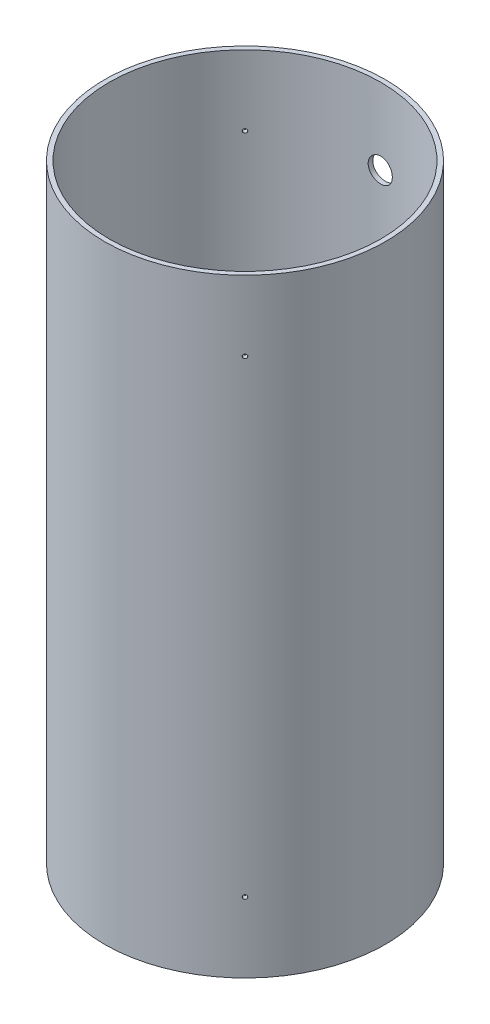
SolidWorks part; units mm, degrees
material "A-Glass Fiber"
ref_plane "Front Plane" through (0, 0, 0) normal (0, 0, 1) x (1, 0, 0)
ref_plane "Top Plane" through (0, 0, 0) normal (0, 1, 0) x (1, 0, 0)
ref_plane "Right Plane" through (0, 0, 0) normal (1, 0, 0) x (0, 0, -1)
sketch "Sketch1" plane through (0, 0, 0) normal (0, 1, 0) x (1, 0, 0)
  circle A0 centre (0, 0) radius 76.1746
  circle A1 centre (0, 0) radius 73.66
  dimension "D1" = 152.3492
  dimension "D2" = 147.32
extrude "Boss-Extrude1" add sketch "Sketch1" along normal blind 330.2
sketch "Sketch4" plane through (0, 0, 0) normal (0, 0, 1) x (1, 0, 0)
  line L0 (-76.1746, 0) -> (76.1746, 0) construction
  line L1 (76.1746, 330.2) -> (-76.1746, 330.2) construction
  line L2 (0, 330.2) -> (0, 0) construction
  line L3 (73.66, 330.2) -> (-73.66, 330.2) construction
  point P0 (0, 41.275)
  point P3 (0, 288.925)
  dimension "D1" = 41.275
  dimension "D2" = 41.275
hole_wizard "1/2 Clearance Hole5" positions "Sketch16" profile "Sketch17" hole size "1/2" standard "ANSI Inch"
sketch "Sketch16" plane through (0, 0, 0) normal (0, 0, 1) x (1, 0, 0)
  point P0 (0, 288.925)
sketch "Sketch17" plane through (0, 288.925, 0) normal (1, 0, 0) x (0, -1, 0)
  line L0 (0, 0) -> (0, 80.1345)
  line L1 (0, 80.1345) -> (6.5481, 76.2)
  line L2 (6.5481, 76.2) -> (6.5481, 0)
  line L5 (6.5481, 0) -> (0, 0)
  line L10 (0, 80.1345) -> (-6.5481, 76.2) construction
  line L11 (0, -6.35) -> (0, 107.95) construction
  dimension "Hole Dia." = 13.0962
  dimension "Hole Depth" = 76.2
  dimension "Drill Angle" = 118
hole_wizard "1/2 Clearance Hole7" positions "Sketch20" profile "Sketch21" hole size "1/2" standard "ANSI Inch"
sketch "Sketch20" plane through (0, 0, 0) normal (0, 0, 1) x (1, 0, 0)
  point P0 (0, 41.275)
sketch "Sketch21" plane through (0, 41.275, 0) normal (1, 0, 0) x (0, -1, 0)
  line L0 (0, 0) -> (0, 80.1345)
  line L1 (0, 80.1345) -> (6.5481, 76.2)
  line L2 (6.5481, 76.2) -> (6.5481, 0)
  line L5 (6.5481, 0) -> (0, 0)
  line L10 (0, 80.1345) -> (-6.5481, 76.2) construction
  line L11 (0, -6.35) -> (0, 107.95) construction
  dimension "Hole Dia." = 13.0962
  dimension "Hole Depth" = 76.2
  dimension "Drill Angle" = 118
ref_plane "Plane1" through (0, 0, 0) normal (-0.7071, 0, 0.7071) x (0.7071, 0, 0.7071)
sketch "Sketch23" plane through (0, 0, 0) normal (-0.7071, 0, 0.7071) x (0.7071, 0, 0.7071)
  line L0 (0, 0) -> (0, 330.2) construction
  line L1 (73.66, 330.2) -> (-73.66, 330.2) construction
  line L2 (-76.1746, 165.1) -> (76.1746, 165.1) construction
  line L3 (76.1746, 0) -> (76.1746, 330.2) construction
  circle A0 centre (0, 292.1) radius 1.0922
  circle A1 centre (0, 38.1) radius 1.0922
  point P12 (0, 165.1)
  dimension "D3" = 2.1844
  dimension "D1" = 127
  dimension "D2" = 127
extrude "Shear Scrrews" cut sketch "Sketch23" against normal through all
pattern_circular "CirPattern1" count 4 over 360 about axis through (0, 330.2, 0) along (0, -1, 0) of "Shear Scrrews"
equation "\"Mid_Coupler_Length\" = 13in"
equation "\"D1@Boss-Extrude1\"=\"Mid_Coupler_Length\""
equation "\"Shear_Screw_Coupler_Location\" = 4.5in"
equation "\"D1@Sketch23\"=\"Shear_Screw_Coupler_Location\"+0.5"
equation "\"Shear_Screw_Diameter\" = 0.086in"
equation "\"D2@Sketch23\"=\"Shear_Screw_Coupler_Location\"+0.5"
equation "\"D3@Sketch23\"=\"Shear_Screw_Diameter\""
